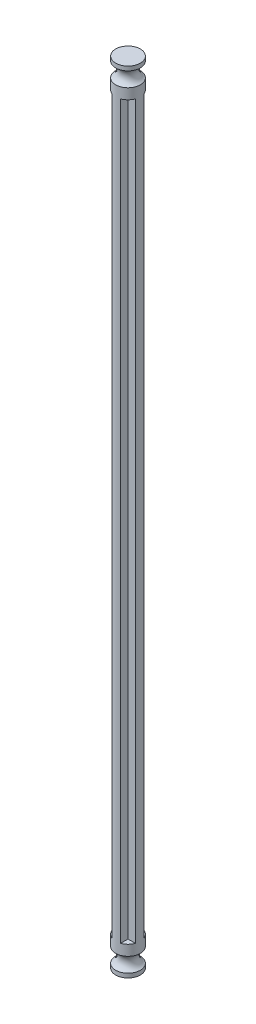
SolidWorks part; units mm, degrees
ref_plane "前视基准面" through (0, 0, 0) normal (0, 0, 1) x (1, 0, 0)
ref_plane "上视基准面" through (0, 0, 0) normal (0, 1, 0) x (1, 0, 0)
ref_plane "右视基准面" through (0, 0, 0) normal (1, 0, 0) x (0, 0, -1)
sketch "草图1" plane through (0, 0, 0) normal (0, 1, 0) x (1, 0, 0)
  line L0 (1, 1) -> (1, 2.7753)
  line L7 (1, 1) -> (2.7753, 1)
  line L8 (1, -1) -> (2.7753, -1)
  line L9 (1, -1) -> (1, -2.7753)
  line L10 (-1, -1) -> (-1, -2.7753)
  line L11 (-1, -1) -> (-2.7753, -1)
  line L12 (-1, 1) -> (-2.7753, 1)
  line L13 (-1, 1) -> (-1, 2.7753)
  arc A0 (-2.7753, 1) -> (-2.7753, -1) centre (0, 0) ccw
  arc A1 (-1, -2.7753) -> (1, -2.7753) centre (0, 0) ccw
  arc A2 (2.7753, -1) -> (2.7753, 1) centre (0, 0) ccw
  arc A3 (1, 2.7753) -> (-1, 2.7753) centre (0, 0) ccw
  dimension "D1" = 5.9
  dimension "D2" = 2
  dimension "D3" = 2
  dimension "D4" = 2
  dimension "D5" = 2
  dimension "D6" = 1
  dimension "D7" = 1
  dimension "D8" = 1
  dimension "D9" = 1
extrude "凸台-拉伸2" add sketch "草图1" along normal blind 175.28
sketch "草图3" plane through (0, 0, 0) normal (1, 0, 0) x (0, 0, -1)
  line L0 (0, 175.28) -> (0, 182.28)
  line L1 (1, 175.28) -> (-1, 175.28) construction
  line L2 (0, 182.28) -> (2.95, 182.28)
  line L3 (0, 175.28) -> (2.95, 175.28)
  line L4 (2.95, 175.28) -> (2.95, 177.78)
  line L5 (2.95, 182.28) -> (2.95, 181.28)
  line L6 (0, 0) -> (0, -7)
  line L7 (0, -7) -> (2.95, -7)
  line L8 (0, 0) -> (2.95, 0)
  line L9 (2.95, 0) -> (2.95, -2.5)
  line L10 (2.95, -7) -> (2.95, -6)
  arc A0 (2.95, 181.28) -> (2.95, 177.78) centre (3.9182, 179.53) ccw
  arc A1 (2.95, -2.5) -> (2.95, -6) centre (3.9182, -4.25) ccw
  dimension "D5" = 1
  dimension "D4" = 2
  dimension "D9" = 2
  dimension "D1" = 2.95
  dimension "D2" = 7
  dimension "D3" = 2.5
  dimension "D6" = 7
  dimension "D7" = 2.5
  dimension "D8" = 1
revolve "旋转3" add sketch "草图3" angle 360 about L6
